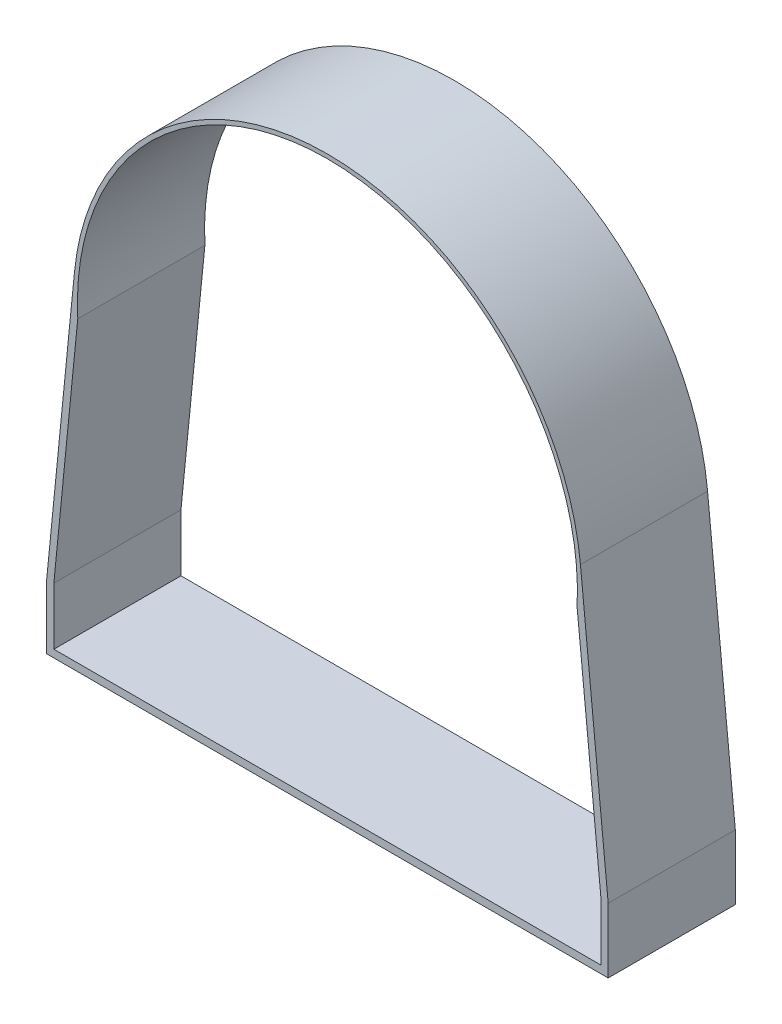
SolidWorks part; units mm, degrees
ref_plane "Front Plane" through (0, 0, 0) normal (0, 0, 1) x (1, 0, 0)
ref_plane "Top Plane" through (0, 0, 0) normal (0, 1, 0) x (1, 0, 0)
ref_plane "Right Plane" through (0, 0, 0) normal (1, 0, 0) x (0, 0, -1)
sketch "Sketch1" plane through (0, 0, 0) normal (0, 0, 1) x (1, 0, 0)
  line L0 (-37.9138, 3.7623) -> (-42.0679, -38.1)
  line L1 (37.9138, 3.7623) -> (42.0679, -38.1)
  line L2 (-37.4123, -1.9871) -> (-40.9959, -38.1)
  line L3 (37.4123, -1.9871) -> (40.9959, -38.1)
  line L4 (-40.9959, -38.1) -> (-40.9959, -46.6725)
  line L5 (40.9959, -38.1) -> (40.9959, -46.6725)
  line L6 (-42.0679, -38.1) -> (-42.0679, -47.8075)
  line L7 (-42.0679, -47.8075) -> (42.0679, -47.8075)
  line L8 (42.0679, -47.8075) -> (42.0679, -38.1)
  line L9 (-40.9959, -46.6725) -> (40.9959, -46.6725)
  circle A0 centre (0, 0) radius 38.1 construction
  arc A1 (37.9138, 3.7623) -> (-37.9138, 3.7623) centre (0, 0) ccw
  arc A2 (-37.4123, -1.9871) -> (37.4123, -1.9871) centre (0, 0) cw
  point P14 (0, 0)
extrude "Boss-Extrude1" add sketch "Sketch1" along normal blind 19.05
